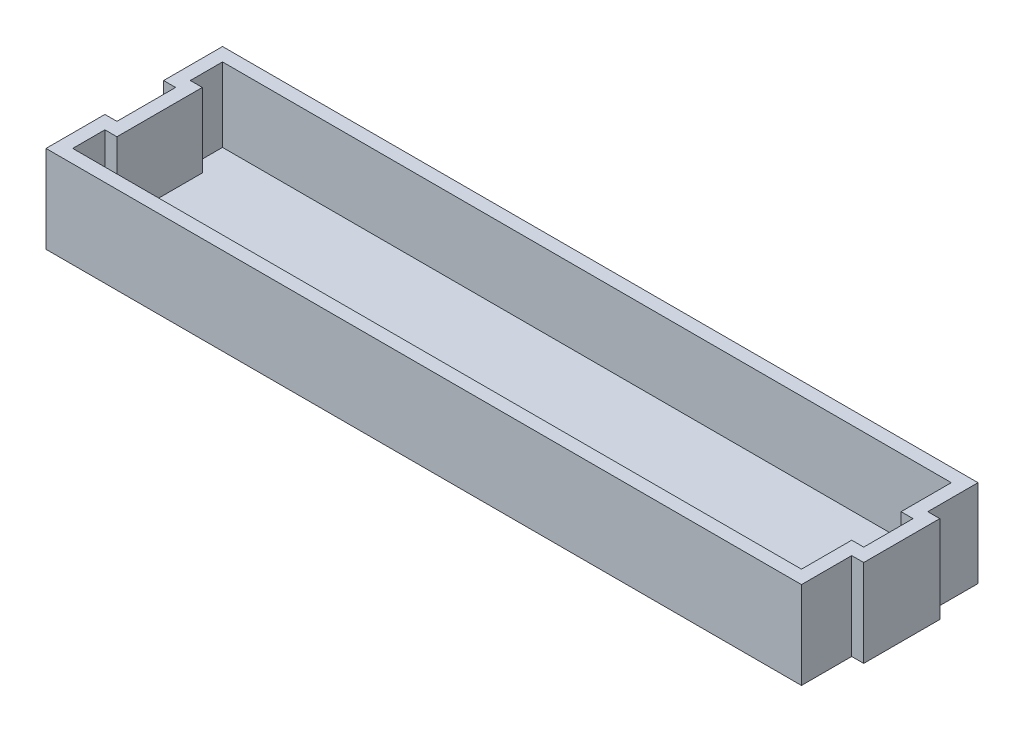
SolidWorks part; units mm, degrees
ref_plane "Front" through (0, 0, 0) normal (0, 0, 1) x (1, 0, 0)
ref_plane "Top" through (0, 0, 0) normal (0, 1, 0) x (1, 0, 0)
ref_plane "Right" through (0, 0, 0) normal (1, 0, 0) x (0, 0, -1)
sketch "Sketch1" plane through (0, 0, 0) normal (0, 1, 0) x (1, 0, 0)
  line L0 (28.31, 6.615) -> (28.31, 2.85)
  line L1 (-28.31, 6.615) -> (28.31, 6.615)
  line L2 (-28.31, 6.615) -> (-28.31, -6.615) construction
  line L3 (-28.31, -6.615) -> (28.31, -6.615)
  line L4 (28.31, 6.615) -> (28.31, -6.615) construction
  line L5 (28.31, 2.85) -> (29.21, 2.85)
  line L6 (29.21, 2.85) -> (29.21, -2.85)
  line L7 (29.21, -2.85) -> (28.31, -2.85)
  line L8 (28.31, -2.85) -> (28.31, -6.615)
  line L9 (-28.31, 6.615) -> (-28.31, 2.2)
  line L10 (-28.31, 2.2) -> (-27.41, 2.2)
  line L11 (-27.41, 2.2) -> (-27.41, -2.2)
  line L12 (-27.41, -2.2) -> (-28.31, -2.2)
  line L13 (-28.31, -2.2) -> (-28.31, -6.615)
extrude "Boss-Extrude1" add sketch "Sketch1" along normal blind 6.55
shell "Shell1" thickness 1
sketch "Sketch2" plane through (0, 0, 0) normal (0, 1, 0) x (1, 0, 0)
  line L0 (-34.5, -9) -> (-34.5, -16) construction
  line L1 (-34.5, -9) -> (34.5, -9)
  line L2 (-34.5, -9) -> (-34.5, 67.5) construction
  line L3 (-34.5, 67.5) -> (34.5, 67.5) construction
  line L4 (34.5, -9) -> (34.5, 67.5) construction
  line L5 (-34.5, -16) -> (34.5, -16) construction
  line L6 (34.5, -16) -> (34.5, -9) construction
  line L7 (34.5, -9) -> (34.5, 36)
  line L8 (34.5, 36) -> (32, 36) construction
  line L9 (32, 36) -> (32, 46.75) construction
  line L10 (32, 46.75) -> (30, 46.75) construction
  line L11 (30, 46.75) -> (30, 67.5) construction
  line L12 (30, 67.5) -> (-31.3, 67.5)
  line L13 (-31.3, 67.5) -> (-31.3, 40.5) construction
  line L14 (-31.3, 40.5) -> (-34.5, 40.5) construction
  line L15 (-34.5, 40.5) -> (-34.5, -9)
  line L16 (30, 67.5) -> (30, 47.75)
  line L17 (31, 46.75) -> (32, 46.75)
  line L18 (32, 46.75) -> (32, 37)
  line L19 (32.94, 36) -> (34.5, 36)
  line L20 (-31.3, 67.5) -> (-31.3, 41.5)
  line L21 (-32.2185, 40.5) -> (-34.5, 40.5)
  arc A0 (30, 47.75) -> (31, 46.75) centre (31, 47.75) ccw
  arc A1 (32, 37) -> (32.94, 36) centre (33.0019, 37) ccw
  arc A2 (-31.3, 41.5) -> (-32.2185, 40.5) centre (-32.3036, 41.5) cw
